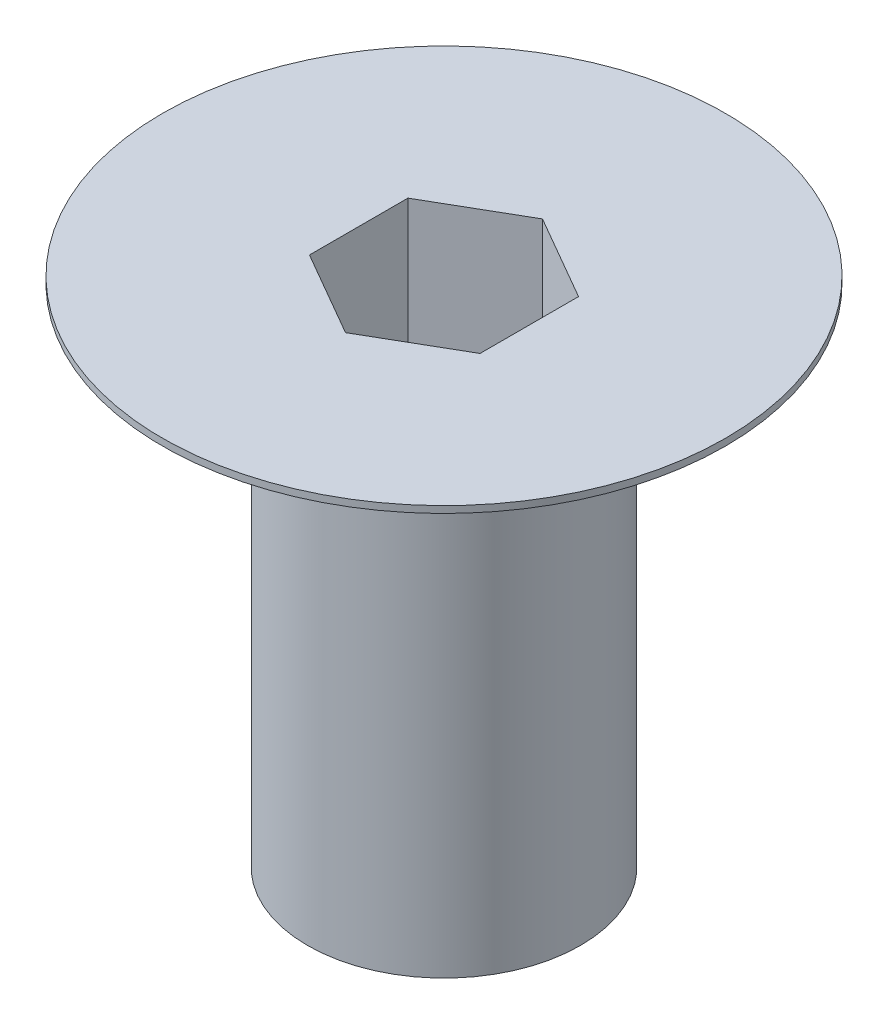
SolidWorks part; units mm, degrees
ref_plane "Plano frontal" through (0, 0, 0) normal (0, 0, 1) x (1, 0, 0)
ref_plane "Plano superior" through (0, 0, 0) normal (0, 1, 0) x (1, 0, 0)
ref_plane "Plano direito" through (0, 0, 0) normal (1, 0, 0) x (0, 0, -1)
sketch "Esboço1" plane through (0, 0, 0) normal (0, 0, 1) x (1, 0, 0)
  line L0 (0, 0) -> (4, 0)
  line L1 (4, 0) -> (4, 12.3463)
  line L2 (8.25, 15) -> (8.25, 14.8)
  line L3 (8.25, 15) -> (0, 15)
  line L4 (0, 15) -> (0, 0) construction
  line L5 (0, 0) -> (0, 15)
  line L6 (8.25, 14.8) -> (4, 12.3463)
  dimension "D1" = 8
  dimension "D2" = 16.5
  dimension "D3" = 60
  dimension "D4" = 0.2
  dimension "D5" = 15
revolve "Revolução1" add sketch "Esboço1" angle 360 about L4
sketch "Esboço2" plane through (0, 15, 0) normal (0, 1, 0) x (1, 0, 0)
  line L1 (0, 2.8868) -> (-2.5, 1.4434)
  line L2 (-2.5, 1.4434) -> (-2.5, -1.4434)
  line L3 (-2.5, -1.4434) -> (0, -2.8868)
  line L4 (0, -2.8868) -> (2.5, -1.4434)
  line L5 (2.5, -1.4434) -> (2.5, 1.4434)
  line L6 (2.5, 1.4434) -> (0, 2.8868)
  circle A0 centre (0, 0) radius 2.5 construction
  dimension "D1" = 5
extrude "Corte-extrusão1" cut sketch "Esboço2" against normal blind 4 contours L5 L6 L1 L2 L3 L4
